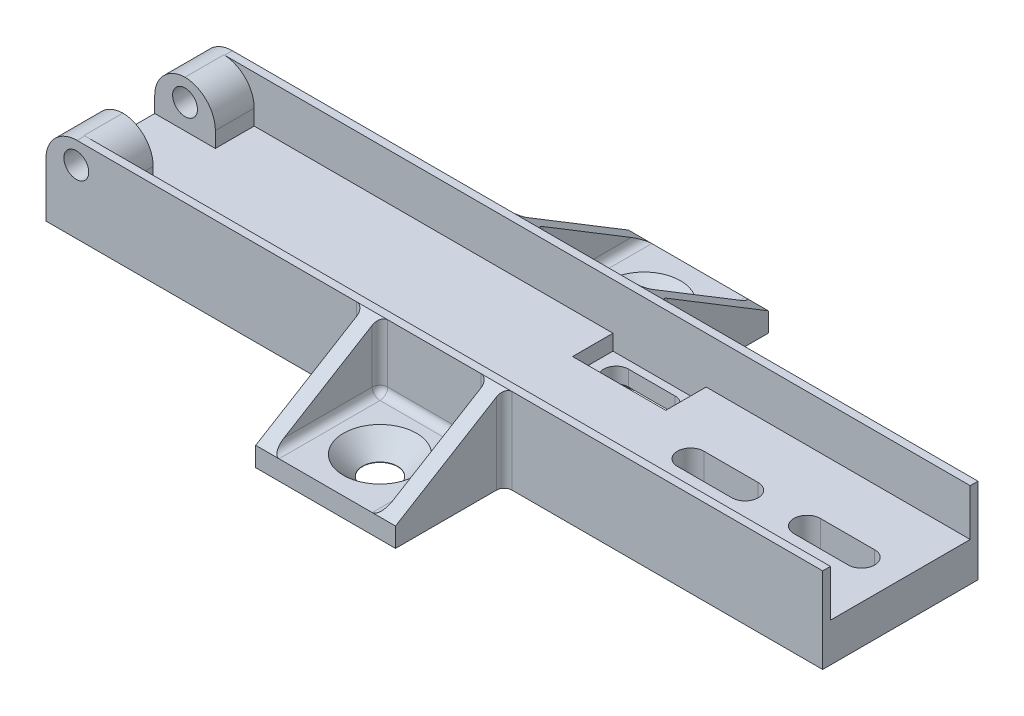
SolidWorks part; units mm, degrees
ref_plane "Ebene vorne" through (0, 0, 0) normal (0, 0, 1) x (1, 0, 0)
ref_plane "Ebene oben" through (0, 0, 0) normal (0, 1, 0) x (1, 0, 0)
ref_plane "Ebene rechts" through (0, 0, 0) normal (1, 0, 0) x (0, 0, -1)
sketch "Sketch1" plane through (0, 0, 0) normal (0, 1, 0) x (1, 0, 0)
  line L0 (-50, -9) -> (-50, 9)
  line L1 (-50, -9) -> (50, -9)
  line L2 (-50, 9) -> (50, 9)
  line L3 (50, -9) -> (50, 9)
  line L4 (-50, -9) -> (50, 9) construction
  line L5 (-50, 9) -> (50, -9) construction
  point P1 (0, 0)
  dimension "D1" = 18
  dimension "D2" = 100
extrude "Boss-Extrude1" add sketch "Sketch1" along normal blind 5
sketch "Sketch2" plane through (0, 5, 0) normal (0, 1, 0) x (1, 0, 0)
  line L0 (-50, -9) -> (50, -9) construction
  line L1 (-50, 9) -> (-42.1952, 9)
  line L2 (-50, 9) -> (-50, -9)
  line L3 (-50, -9) -> (-42.1952, -9)
  line L4 (-42.1952, 9) -> (-42.1952, -9)
extrude "Boss-Extrude2" add sketch "Sketch2" along normal blind 6
fillet "Fillet1" radius 4 1 edges at (-42.1952, 11, 0)
sketch "Sketch4" plane through (0, 11, 0) normal (0, 1, 0) x (1, 0, 0)
  line L0 (-42.1952, 0) -> (-50, 0) construction
  line L1 (-42.1952, -9) -> (-42.1952, 9) construction
  line L2 (-50, 9) -> (-50, -9) construction
  line L3 (-50, -4) -> (-42.1952, -4)
  line L4 (-50, -4) -> (-50, 4)
  line L5 (-42.1952, -4) -> (-42.1952, 4)
  line L6 (-50, 4) -> (-42.1952, 4)
  line L7 (-50, -4) -> (-42.1952, 4) construction
  line L8 (-42.1952, -4) -> (-50, 4) construction
  point P7 (-46.0976, 0)
  dimension "D1" = 8
extrude "Cut-Extrude2" cut sketch "Sketch4" against normal up to surface (6 mm away) up to face at (3.9024, 5, 0)
sketch "Sketch5" plane through (0, 0, 0) normal (0, -1, 0) x (1, 0, 0)
  line L0 (45, 0) -> (38, 0) construction
  line L1 (45, -1.7) -> (38, -1.7)
  line L2 (45, 1.7) -> (38, 1.7)
  line L3 (30, 0) -> (23, 0) construction
  line L4 (30, -1.7) -> (23, -1.7)
  line L5 (30, 1.7) -> (23, 1.7)
  line L7 (50, 9) -> (50, -9) construction
  arc A0 (45, -1.7) -> (45, 1.7) centre (45, 0) ccw
  arc A1 (38, 1.7) -> (38, -1.7) centre (38, 0) ccw
  arc A2 (30, -1.7) -> (30, 1.7) centre (30, 0) ccw
  arc A3 (23, 1.7) -> (23, -1.7) centre (23, 0) ccw
  point P3 (41.5, 0)
  point P8 (26.5, 0)
  dimension "D2" = 15
  dimension "^3,4" = 3.4
  dimension "D3" = 3.4
  dimension "D4" = 5
  dimension "D5" = 7
  dimension "D6" = 7
extrude "Cut-Extrude3" cut sketch "Sketch5" against normal up to surface (5 mm away) up to face at (-21.0976, 5, 0)
sketch "Sketch6" plane through (0, 5, 0) normal (0, 1, 0) x (1, 0, 0)
  line L0 (-50, 4) -> (-50, -4) construction
  line L1 (-26, 9) -> (-26, -9) construction
  line L2 (50, 9) -> (-42.1952, 9) construction
  line L3 (-42.1952, -9) -> (50, -9) construction
  circle A0 centre (-26, 0) radius 2.5
  point P10 (-26, 0)
  dimension "D1" = 5
  dimension "D2" = 24
extrude "Boss-Extrude3" [suppressed] add sketch "Sketch6" along normal blind 15
sketch "Sketch8" plane through (0, 0, 9) normal (0, 0, 1) x (1, 0, 0)
  line L1 (50, 0) -> (-50, 0)
  line L2 (50, 0) -> (50, 11)
  line L3 (50, 11) -> (-50, 11)
  line L4 (-50, 0) -> (-50, 11)
extrude "Boss-Extrude5" add sketch "Sketch8" along normal blind 1
mirror "Mirror1" about plane through (0, 0, 0) normal (0, 0, 1) of "Boss-Extrude5"
sketch "Sketch3" plane through (0, 0, 10) normal (0, 0, 1) x (1, 0, 0)
  line L0 (-42.1952, 7) -> (-42.1952, 5) construction
  line L1 (-42.1952, 8.2) -> (-50, 8.2) construction
  line L4 (-42.1952, 7) -> (-42.1952, 5) construction
  line L5 (-42.1952, 5) -> (-42.1952, 11) construction
  line L6 (50, 11) -> (-50, 11) construction
  line L7 (-50, 11) -> (-50, 0) construction
  circle A0 centre (-46.0976, 8.2) radius 1.6
  arc A1 (-42.1952, 7) -> (-46.1952, 11) centre (-46.1952, 7) ccw construction
  arc A2 (-42.1952, 7) -> (-46.1952, 11) centre (-46.1952, 7) ccw construction
  point P4 (0, 0)
  dimension "D1" = 3.2
  dimension "D2" = 3.2
extrude "Cut-Extrude1" cut sketch "Sketch3" against normal through all
fillet "Fillet2" radius 4 2 edges at (-50, 11, 7) (-50, 11, -7)
sketch "Sketch9" plane through (0, 0, 10) normal (0, 0, 1) x (1, 0, 0)
  line L0 (-50, 0) -> (50, 0) construction
  line L1 (-9, 0) -> (9, 0)
  line L2 (-9, 0) -> (-9, 2.5)
  line L3 (-9, 2.5) -> (9, 2.5)
  line L4 (9, 0) -> (9, 2.5)
  dimension "D1" = 2.5
  dimension "D2" = 18
extrude "Boss-Extrude6" add sketch "Sketch9" along normal blind 14
ref_plane "Plane1" through (0, 0, 0) normal (-1, 0, 0) x (0, 0, 1)
sketch "Sketch10" plane through (9, 0, 0) normal (1, 0, 0) x (0, 0, -1)
  line L0 (-10, 11) -> (-24, 2.5)
  line L1 (-24, 2.5) -> (-10, 2.5) construction
  line L2 (-24, 2.5) -> (-10, 2.5)
  line L3 (-10, 0) -> (-10, 11) construction
  line L4 (-10, 2.5) -> (-10, 11)
extrude "Boss-Extrude7" add sketch "Sketch10" against normal blind 2
mirror "Mirror2" about plane through (0, 0, 0) normal (-1, 0, 0) of "Boss-Extrude7"
hole_wizard "CSK for M4 Countersunk Flat Head Screw1" positions "Sketch13" profile "Sketch12" countersink size "M4" standard "DIN" end condition up to next
sketch "Sketch13" plane through (0, 2.5, 0) normal (0, 1, 0) x (1, 0, 0)
  line L0 (7, -17) -> (-7, -17) construction
  line L1 (7, -24) -> (7, -10) construction
  line L2 (-7, -24) -> (-7, -10) construction
  point P9 (0, -17)
sketch "Sketch12" plane through (0, 2.5, 17) normal (1, 0, 0) x (0, 0, 1)
  line L0 (0, 0) -> (0, 2.501)
  line L1 (0, 2.501) -> (2.25, 2.501)
  line L2 (2.25, 2.501) -> (2.25, 2.45)
  line L3 (2.25, 2.45) -> (4.7, 0)
  line L5 (4.7, 0) -> (0, 0)
  line L6 (-2.25, 2.45) -> (-4.7, 0) construction
  line L11 (0, -6.35) -> (0, 107.95) construction
  dimension "Thru Hole Dia." = 4.5
  dimension "Thru Hole Depth" = 2.501
  dimension "Near C'Sink Dia." = 9.4
  dimension "Near C'Sink Angle" = 90
mirror "Mirror5" about plane through (0, 0, 0) normal (0, 0, 1) of "CSK for M4 Countersunk Flat Head Screw1", "Mirror2", "Boss-Extrude7", "Boss-Extrude6"
fillet "Fillet4" radius 1 14 edges at (-7, 6.75, 10) (7, 6.75, 10) (9, 5.5, 10) (-9, 5.5, 10) (-7, 2.5, 17) (7, 2.5, 17) (0, 2.5, 10) (9, 5.5, -10) (-9, 5.5, -10) (7, 6.75, -10) (-7, 6.75, -10) (0, 2.5, -10) (-7, 2.5, -17) (7, 2.5, -17)
sketch "Sketch14" plane through (0, 5, 0) normal (0, 1, 0) x (1, 0, 0)
  line L0 (13, -6.4) -> (7, -6.4) construction
  line L1 (13, -8) -> (7, -8)
  line L2 (13, -4.8) -> (7, -4.8)
  line L4 (0, 0) -> (19.2609, 0) construction
  line L5 (13, 6.4) -> (7, 6.4) construction
  line L6 (13, 8) -> (7, 8)
  line L7 (13, 4.8) -> (7, 4.8)
  line L8 (-42.1952, -9) -> (50, -9) construction
  arc A0 (13, -8) -> (13, -4.8) centre (13, -6.4) ccw
  arc A1 (7, -4.8) -> (7, -8) centre (7, -6.4) ccw
  arc A2 (13, 8) -> (13, 4.8) centre (13, 6.4) cw
  arc A3 (7, 4.8) -> (7, 8) centre (7, 6.4) cw
  point P2 (10, -6.4)
  point P14 (10, 6.4)
  dimension "D1" = 10
  dimension "D2" = 6
  dimension "D3" = 3.2
  dimension "D4" = 2.6
extrude "Cut-Extrude4" cut sketch "Sketch14" against normal up to next
chamfer "Chamfer1" distance 1 angle 45 16 edges at (10, 0, -4.8) (5.4, 0, -6.4) (14.6, 0, -6.4) (5.4, 0, 6.4) (14.6, 0, 6.4) (10, 0, 4.8) (26.5, 0, 1.7) (21.3, 0, 0) (31.7, 0, 0) (26.5, 0, -1.7) (41.5, 0, 1.7) (36.3, 0, 0) (46.7, 0, 0) (41.5, 0, -1.7) (10, 0, 8) (10, 0, -8)
sketch "Sketch15" plane through (0, 5, 0) normal (0, 1, 0) x (1, 0, 0)
  line L0 (19.0521, 0) -> (-5.2162, 0) construction
  line L1 (16, 9) -> (4, 9)
  line L2 (16, 9) -> (16, 3.8)
  line L3 (16, 3.8) -> (4, 3.8)
  line L4 (4, 9) -> (4, 3.8)
  line L5 (16, -9) -> (4, -9)
  line L6 (4, -9) -> (4, -3.8)
  line L7 (16, -3.8) -> (4, -3.8)
  line L8 (16, -9) -> (16, -3.8)
  line L9 (10, 4.8) -> (10, 3.8) construction
  line L10 (7, 4.8) -> (13, 4.8) construction
  line L12 (-42.1952, -9) -> (50, -9)
  line L13 (50, -9) -> (50, 9)
  line L14 (50, 9) -> (-42.1952, 9)
  line L17 (-42.1952, 9) -> (-42.1952, 4)
  line L18 (-42.1952, 4) -> (-50, 4)
  line L19 (-50, 4) -> (-50, -4)
  line L20 (-50, -4) -> (-42.1952, -4)
  line L21 (-42.1952, -4) -> (-42.1952, -9)
  line L24 (-42.1952, -9) -> (50, -9) construction
  line L25 (50, -9) -> (50, 9) construction
  line L26 (50, 9) -> (-42.1952, 9) construction
  line L29 (-42.1952, 9) -> (-42.1952, 4) construction
  line L30 (-42.1952, 4) -> (-50, 4) construction
  line L31 (-50, 4) -> (-50, -4) construction
  line L32 (-50, -4) -> (-42.1952, -4) construction
  line L33 (-42.1952, -4) -> (-42.1952, -9) construction
  point P3 (10, 3.8)
  dimension "D2" = 5.2
  dimension "D3" = 12
  dimension "D1" = 0
extrude "Cut-Extrude5" cut sketch "Sketch15" against normal blind 2
